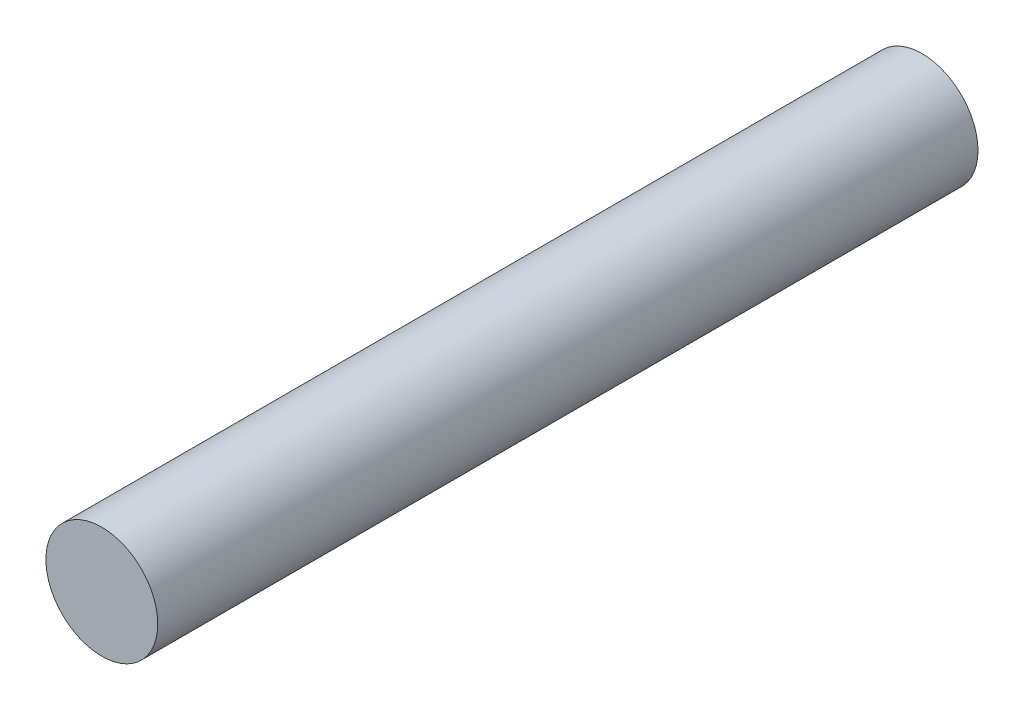
SolidWorks part; units mm, degrees
ref_plane "前视基准面" through (0, 0, 0) normal (0, 0, 1) x (1, 0, 0)
ref_plane "上视基准面" through (0, 0, 0) normal (0, 1, 0) x (1, 0, 0)
ref_plane "右视基准面" through (0, 0, 0) normal (1, 0, 0) x (0, 0, -1)
sketch "草图1" plane through (0, 0, 0) normal (0, 0, 1) x (1, 0, 0)
  circle A0 centre (0, 0) radius 1.5
  dimension "D1" = 3
extrude "凸台-拉伸1" add sketch "草图1" along normal blind 22
